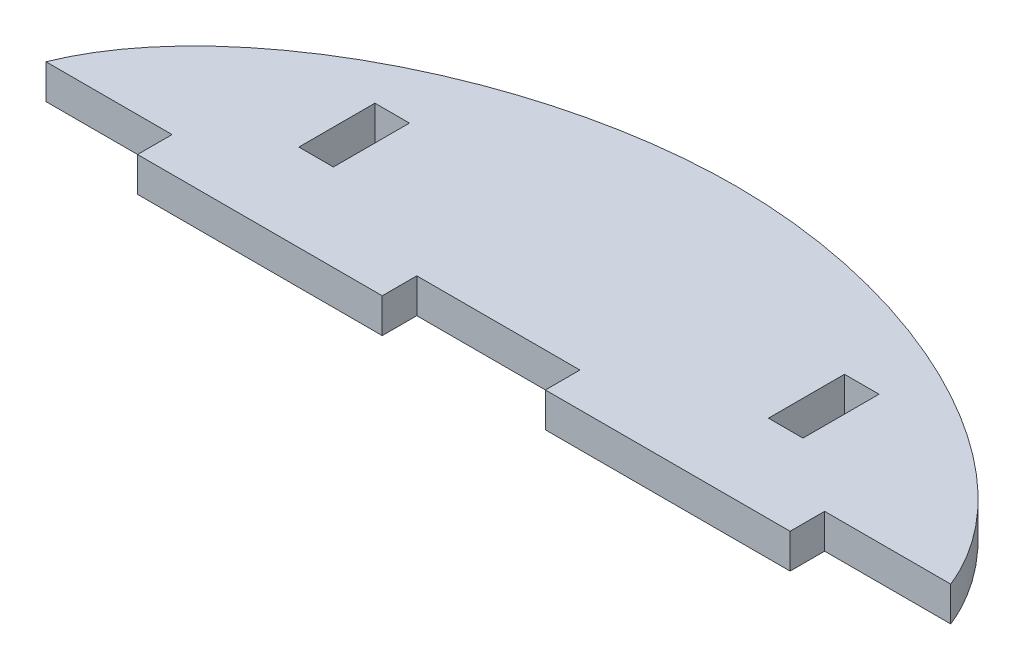
SolidWorks part; units mm, degrees
ref_plane "Front Plane" through (0, 0, 0) normal (0, 0, 1) x (1, 0, 0)
ref_plane "Top Plane" through (0, 0, 0) normal (0, 1, 0) x (1, 0, 0)
ref_plane "Right Plane" through (0, 0, 0) normal (1, 0, 0) x (0, 0, -1)
sketch "Sketch1" plane through (0, 0, 0) normal (0, 1, 0) x (1, 0, 0)
  line L0 (0, 0) -> (85, 0)
  line L1 (42.5, 0) -> (42.5, 25)
  line L2 (104.8351, -112.4906) -> (65.1649, 112.4906) construction
  line L3 (16.2479, 92.1462) -> (-16.2479, -92.1462) construction
  spline S0 degree 3 poles (0, 0) (2.3153, 13.1308) (42.5, 36.8692) (82.6847, 13.1308) (85, 0) knots 0 0 0 0 0.5 1 1 1 1
  dimension "D4" = 80
  dimension "D5" = 40
  dimension "D6" = 40
  dimension "D1" = 85
  dimension "D2" = 25
  dimension "D3" = 80
extrude "Boss-Extrude1" add sketch "Sketch1" along normal blind 3.175 contours S0 L0 L1 | S0 L1 L0
sketch "Sketch2" plane through (0, 0, 0) normal (0, -1, 0) x (1, 0, 0)
  line L0 (0, 0) -> (85, 0) construction
  line L1 (65.675, -15) -> (62.5, -15)
  line L2 (65.675, -15) -> (65.675, -8.008)
  line L3 (65.675, -8.008) -> (62.5, -8.008)
  line L4 (62.5, -15) -> (62.5, -8.008)
  line L5 (22.5, -15) -> (19.325, -15)
  line L6 (22.5, -15) -> (22.5, -8.008)
  line L7 (22.5, -8.008) -> (19.325, -8.008)
  line L8 (19.325, -15) -> (19.325, -8.008)
  line L9 (85, 0) -> (72.5, 0)
  line L10 (85, 0) -> (85, -3.175)
  line L11 (85, -3.175) -> (72.5, -3.175)
  line L12 (72.5, 0) -> (72.5, -3.175)
  line L13 (0, 0) -> (12.5, 0)
  line L14 (0, 0) -> (0, -3.175)
  line L15 (0, -3.175) -> (12.5, -3.175)
  line L16 (12.5, 0) -> (12.5, -3.175)
  line L18 (50, 0) -> (35, 0)
  line L19 (50, 0) -> (50, -3.175)
  line L20 (50, -3.175) -> (35, -3.175)
  line L21 (35, 0) -> (35, -3.175)
  spline S0 degree 3 poles (0, 0) (2.3153, -13.1308) (42.5, -36.8692) (82.6847, -13.1308) (85, 0) knots 0 0 0 0 0.5 1 1 1 1 construction
  point P24 (42.5, 0)
  point P25 (42.5, -3.175)
  dimension "D1" = 6.992
  dimension "D2" = 6.992
  dimension "D3" = 12.5
  dimension "D4" = 12.5
  dimension "D5" = 15
  dimension "D6" = 3.175
extrude "Cut-Extrude1" cut sketch "Sketch2" against normal through all
